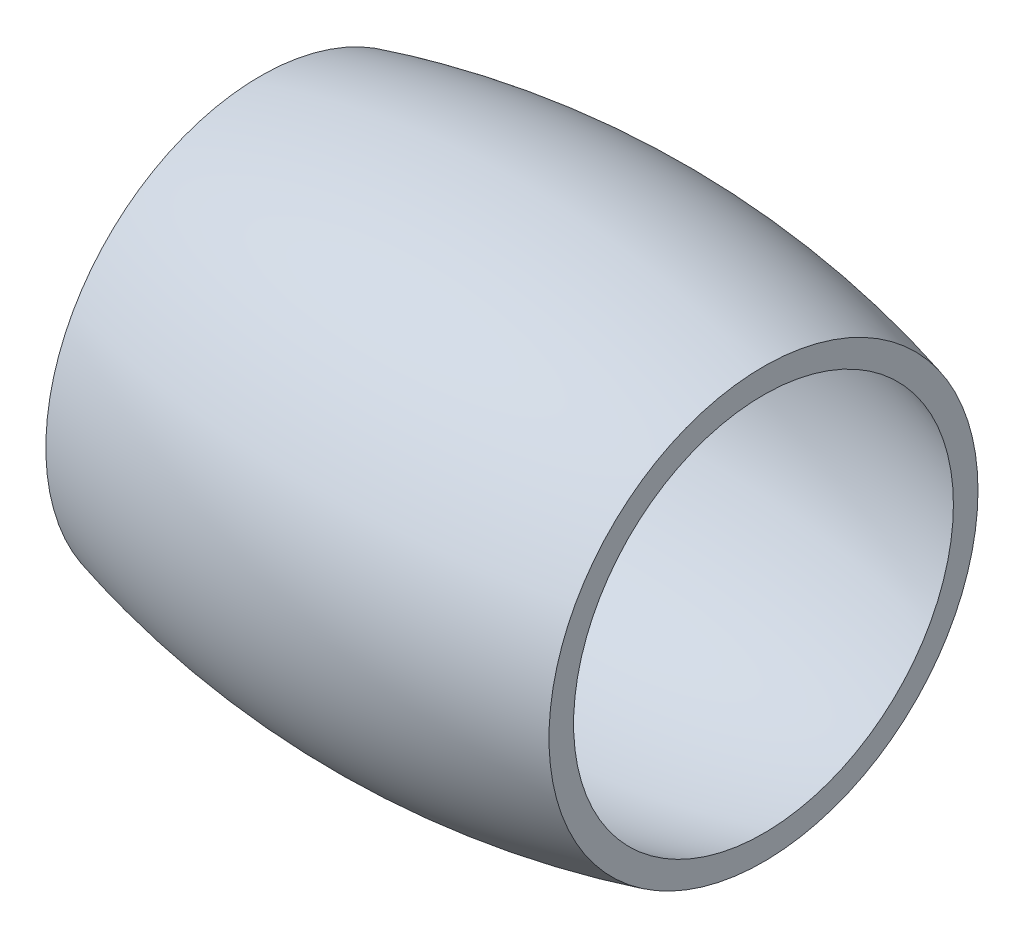
SolidWorks part; units mm, degrees
material "Silicon Rubber"
ref_plane "Front Plane" through (0, 0, 0) normal (0, 0, 1) x (1, 0, 0)
ref_plane "Top Plane" through (0, 0, 0) normal (0, 1, 0) x (1, 0, 0)
ref_plane "Right Plane" through (0, 0, 0) normal (1, 0, 0) x (0, 0, -1)
sketch "Sketch1" plane through (0, 0, 0) normal (0, 0, 1) x (1, 0, 0)
  line L0 (-16.8232, 12.7) -> (-16.8232, 0) construction
  line L1 (-16.8232, 12.7) -> (-16.8232, 0)
  line L2 (16.8232, 12.7) -> (16.8232, 0) construction
  line L3 (16.8232, 12.7) -> (16.8232, 0)
  line L4 (27.967, 0) -> (-27.967, 0) construction
  line L5 (27.967, 0) -> (-27.967, 0)
  circle A0 centre (0, -48.4402) radius 65 construction
  circle A1 centre (0, -48.4402) radius 65
  circle A2 centre (0, -48.4402) radius 63.4125 construction
  circle A3 centre (0, -48.4402) radius 63.4125
sketch "Sketch2" plane through (0, 0, 0) normal (0, 0, 1) x (1, 0, 0)
  line L0 (27.967, 0) -> (-27.967, 0) construction
  line L1 (16.8232, 12.7) -> (16.8232, 0) construction
  line L2 (-16.8232, 12.7) -> (-16.8232, 0) construction
  line L3 (27.967, 0) -> (-27.967, 0) construction
  line L4 (16.8232, 12.7) -> (16.8232, 0) construction
  line L5 (-16.8232, 12.7) -> (-16.8232, 0) construction
  line L6 (-16.8232, 12.7) -> (-16.8232, 14.345)
  line L7 (16.8232, 12.7) -> (16.8232, 14.345)
  line L8 (0, 0) -> (0, 16.5598) construction
  circle A1 centre (0, -48.4402) radius 63.4125
  arc A2 (16.8232, 12.7) -> (-16.8232, 12.7) centre (0, -48.4402) ccw
  circle A3 centre (0, -48.4402) radius 65
  arc A4 (16.8232, 14.345) -> (-16.8232, 14.345) centre (0, -48.4402) ccw
  dimension "D3" = 16.5598
  dimension "D1" = 0
  dimension "D2" = 0
revolve "Revolve1" add sketch "Sketch2" angle 360 about L3
sketch "Sketch3" plane through (0, 0, 0) normal (0, 1, 0) x (1, 0, 0)
  line L0 (0, 0) -> (0, 16.5598) construction
  line L1 (0, 0) -> (0, -16.5598) construction
  arc A0 (16.8232, 14.345) -> (-16.8232, 14.345) centre (0, -48.4402) ccw construction
  arc A1 (-16.8232, -14.345) -> (16.8232, -14.345) centre (0, 48.4402) ccw construction
